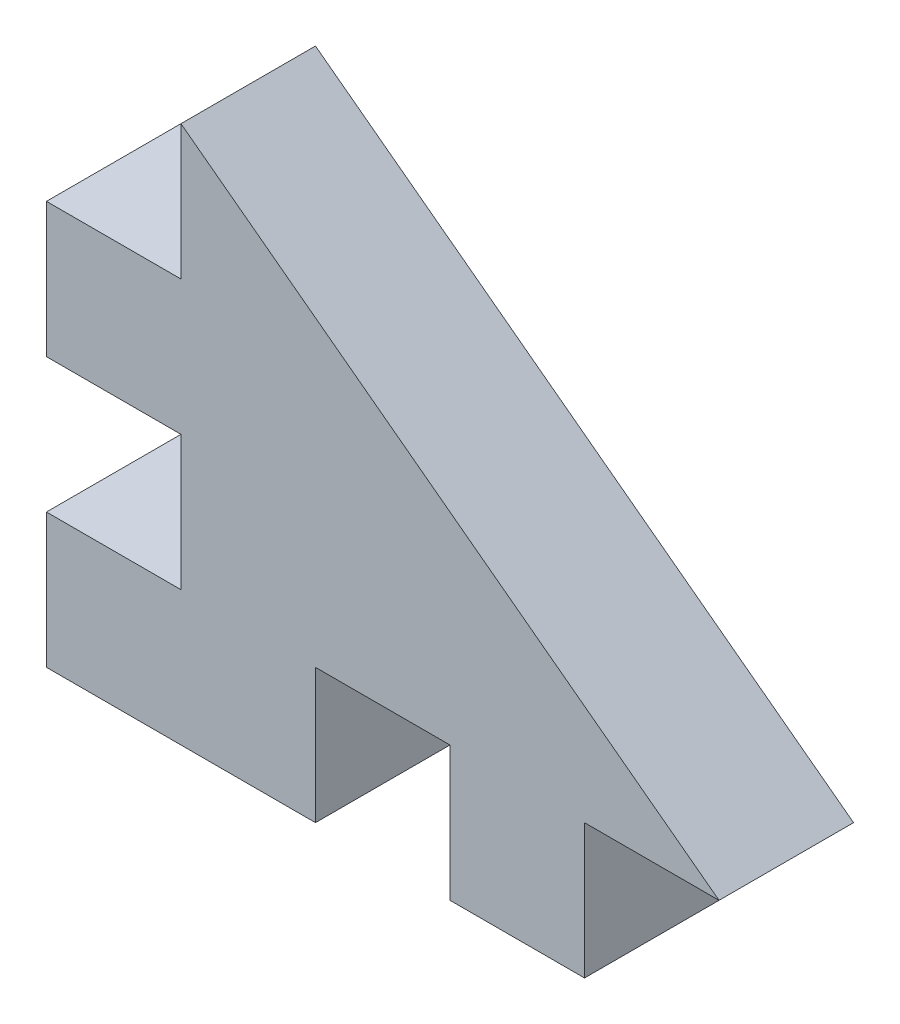
SolidWorks part; units mm, degrees
ref_plane "Plan de face" through (0, 0, 0) normal (0, 0, 1) x (1, 0, 0)
ref_plane "Plan de dessus" through (0, 0, 0) normal (0, 1, 0) x (1, 0, 0)
ref_plane "Plan de droite" through (0, 0, 0) normal (1, 0, 0) x (0, 0, -1)
sketch "Esquisse1" plane through (0, 0, 0) normal (0, 0, 1) x (1, 0, 0)
  line L1 (-43.243, 14.2635) -> (-18.243, 14.2635)
  line L2 (-43.243, 14.2635) -> (-43.243, -5.7365)
  line L3 (-43.243, -5.7365) -> (-18.243, -5.7365)
  line L4 (-18.243, 14.2635) -> (-18.243, -5.7365)
extrude "Boss.-Extru.1" add sketch "Esquisse1" along normal blind 5
sketch "Esquisse2" plane through (0, 0, 5) normal (0, 0, 1) x (1, 0, 0)
  line L0 (-33.243, -5.7365) -> (-28.243, -5.7365)
  line L1 (-43.243, -0.7365) -> (-38.243, -0.7365)
  line L2 (-43.243, -0.7365) -> (-43.243, 4.2635)
  line L3 (-43.243, 4.2635) -> (-38.243, 4.2635)
  line L4 (-38.243, -0.7365) -> (-38.243, 4.2635)
  line L5 (-33.243, -5.7365) -> (-33.243, -0.7365)
  line L6 (-33.243, -0.7365) -> (-28.243, -0.7365)
  line L7 (-28.243, -5.7365) -> (-28.243, -0.7365)
  line L8 (-43.243, 9.2635) -> (-38.243, 9.2635)
  line L9 (-43.243, 9.2635) -> (-43.243, 14.2635)
  line L10 (-43.243, 14.2635) -> (-38.243, 14.2635)
  line L11 (-38.243, 9.2635) -> (-38.243, 14.2635)
  line L12 (-18.243, 14.2635) -> (-43.243, 14.2635) construction
  line L13 (-18.243, 14.2635) -> (-38.243, 14.2635)
  line L14 (-38.243, 14.2635) -> (-18.243, -0.7365)
  line L15 (-18.243, -5.7365) -> (-18.243, 14.2635) construction
  line L16 (-18.243, -0.7365) -> (-18.243, 14.2635)
  line L17 (-43.243, -5.7365) -> (-18.243, -5.7365) construction
  line L18 (-23.243, -5.7365) -> (-18.243, -5.7365)
  line L19 (-23.243, -5.7365) -> (-23.243, -0.7365)
  line L20 (-23.243, -0.7365) -> (-18.243, -0.7365)
  line L21 (-18.243, -5.7365) -> (-18.243, -0.7365)
  line M1 (-43.243, 14.2635) -> (-43.243, -5.7365)
  line M2 (-43.243, -5.7365) -> (-18.243, -5.7365)
  line M3 (-18.243, -5.7365) -> (-18.243, 14.2635)
  line M4 (-18.243, 14.2635) -> (-43.243, 14.2635)
  dimension "D1" = 5
  dimension "D3" = 5
  dimension "D4" = 10
  dimension "D2" = 2
extrude "Enlèv. mat.-Extru.4" cut sketch "Esquisse2" against normal blind 5 contours L14 M4 M3 | L8 L11 M4 M1 | L1 L4 L3 M1 | L7 L6 L5 M2 | L21 L20 L19 M2
